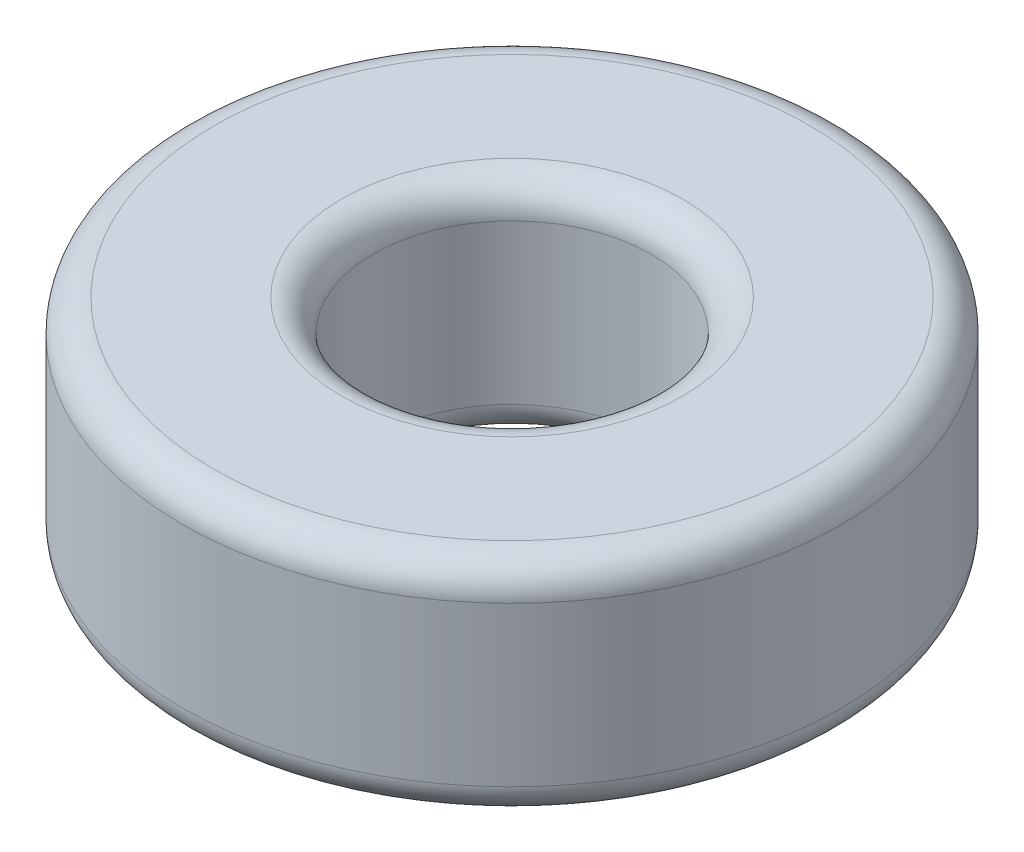
SolidWorks part; units mm, degrees
ref_plane "Front Plane" through (0, 0, 0) normal (0, 0, 1) x (1, 0, 0)
ref_plane "Top Plane" through (0, 0, 0) normal (0, 1, 0) x (1, 0, 0)
ref_plane "Right Plane" through (0, 0, 0) normal (1, 0, 0) x (0, 0, -1)
sketch "Sketch1" plane through (0, 0, 0) normal (0, 1, 0) x (1, 0, 0)
  circle A0 centre (0, 0) radius 2.1844
  circle A1 centre (0, 0) radius 5.1844
  dimension "D1" = 4.3688
  dimension "D2" = 3
extrude "Boss-Extrude1" add sketch "Sketch1" along normal blind 3.5
fillet "Fillet1" radius 0.5 4 edges at (0, 0, 2.1844) (0, 0, 5.1844) (0, 3.5, 2.1844) (0, 3.5, 5.1844)
